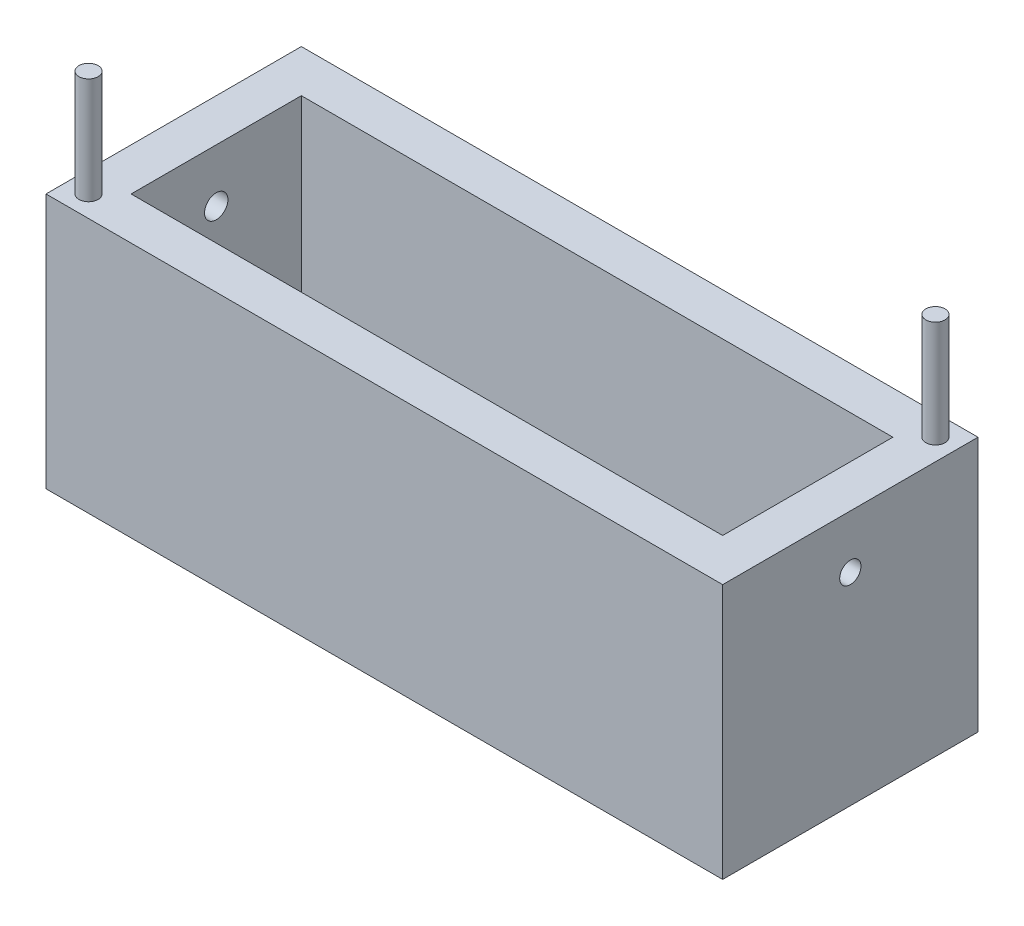
SolidWorks part; units mm, degrees
ref_plane "Front Plane" through (0, 0, 0) normal (0, 0, 1) x (1, 0, 0)
ref_plane "Top Plane" through (0, 0, 0) normal (0, 1, 0) x (1, 0, 0)
ref_plane "Right Plane" through (0, 0, 0) normal (1, 0, 0) x (0, 0, -1)
sketch "Sketch1" plane through (0, 0, 0) normal (0, 0, 1) x (1, 0, 0)
  line L1 (0, 0) -> (-403.86, 0)
  line L2 (0, 0) -> (0, 152.4)
  line L3 (0, 152.4) -> (-403.86, 152.4)
  line L4 (-403.86, 0) -> (-403.86, 152.4)
  dimension "D1" = 152.4
  dimension "D2" = 403.86
extrude "Boss-Extrude1" add sketch "Sketch1" along normal blind 152.4
sketch "Sketch3" plane through (0, 152.4, 0) normal (0, 1, 0) x (1, 0, 0)
  line L0 (-403.86, -152.4) -> (-403.86, 0) construction
  line L1 (-378.46, -25.4) -> (-25.4, -25.4)
  line L2 (-378.46, -25.4) -> (-378.46, -127)
  line L3 (-378.46, -127) -> (-25.4, -127)
  line L4 (-25.4, -25.4) -> (-25.4, -127)
  line L5 (0, 0) -> (-403.86, 0) construction
  line L6 (0, -152.4) -> (0, 0) construction
  line L7 (0, -152.4) -> (-403.86, -152.4) construction
  dimension "D1" = 25.4
  dimension "D2" = 25.4
  dimension "D3" = 25.4
  dimension "D4" = 25.4
extrude "Cut-Extrude1" cut sketch "Sketch3" against normal blind 139.7
sketch "Sketch4" plane through (0, 152.4, 0) normal (0, 1, 0) x (1, 0, 0)
  line L0 (-403.86, -152.4) -> (-403.86, 0) construction
  line L1 (0, -152.4) -> (-403.86, -152.4) construction
  circle A0 centre (-391.16, -139.7) radius 5.715
  dimension "D1" = 11.43
  dimension "D2" = 12.7
  dimension "D3" = 12.7
extrude "Boss-Extrude2" add sketch "Sketch4" along normal blind 63.5
sketch "Sketch5" plane through (0, 0, 0) normal (1, 0, 0) x (0, 0, -1)
  line L0 (-152.4, 0) -> (-152.4, 152.4) construction
  line L1 (-152.4, 152.4) -> (0, 152.4) construction
  circle A0 centre (-76.2, 120.65) radius 6.35
  dimension "D1" = 12.7
  dimension "D2" = 76.2
  dimension "D3" = 31.75
extrude "Cut-Extrude2" cut sketch "Sketch5" against normal blind 63.5
sketch "Sketch6" plane through (-403.86, 0, 0) normal (-1, 0, 0) x (0, 0, 1)
  line L0 (152.4, 152.4) -> (0, 152.4) construction
  line L1 (152.4, 152.4) -> (152.4, 0) construction
  circle A0 centre (76.2, 120.65) radius 6.985
  dimension "D1" = 13.97
  dimension "D2" = 31.75
  dimension "D3" = 76.2
extrude "Cut-Extrude3" cut sketch "Sketch6" against normal up to next
sketch "Sketch7" plane through (0, 152.4, 0) normal (0, 1, 0) x (1, 0, 0)
  line L0 (-25.4, -127) -> (-25.4, -25.4) construction
  line L1 (0, 0) -> (-403.86, 0) construction
  circle A0 centre (-12.7, -12.7) radius 5.715
  dimension "D1" = 11.43
  dimension "D2" = 12.7
  dimension "D3" = 12.7
extrude "Boss-Extrude3" add sketch "Sketch7" along normal blind 63.5
